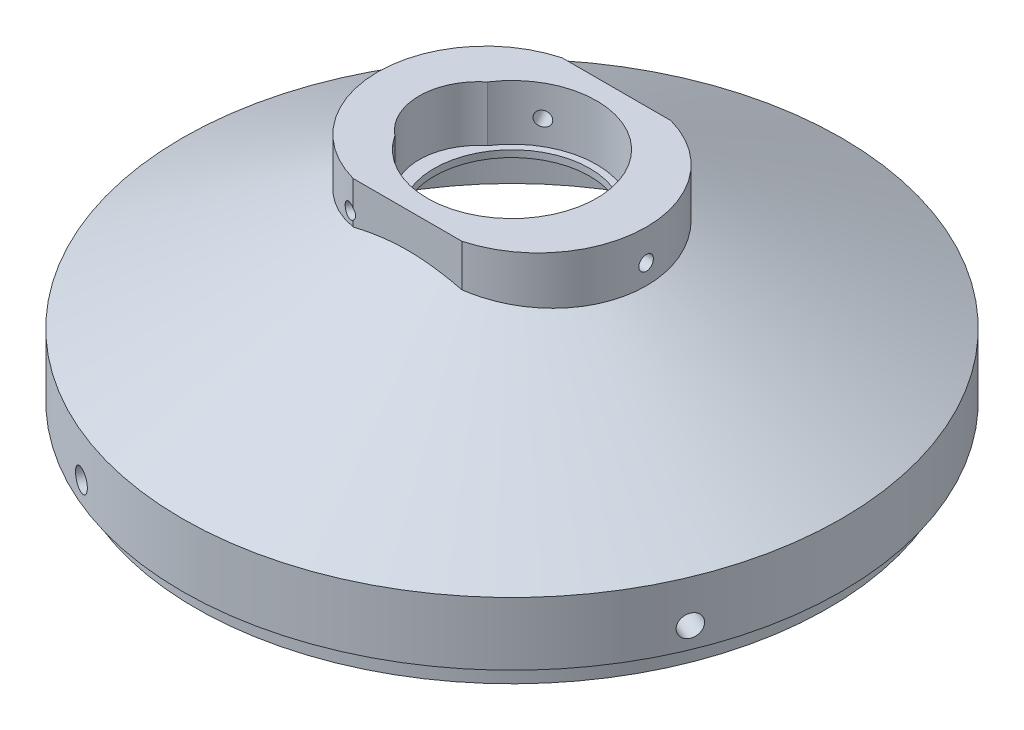
SolidWorks part; units mm, degrees
ref_plane "Front Plane" through (0, 0, 0) normal (0, 0, 1) x (1, 0, 0)
ref_plane "Top Plane" through (0, 0, 0) normal (0, 1, 0) x (1, 0, 0)
ref_plane "Right Plane" through (0, 0, 0) normal (1, 0, 0) x (0, 0, -1)
sketch "Sketch2" plane through (0, 0, 0) normal (0, 0, 1) x (1, 0, 0)
  line L0 (47.675, 0) -> (0, 0) construction
  line L1 (0, 0) -> (0, 12.7) construction
  line L2 (49.7, 12.7) -> (49.7, 3.2004)
  line L3 (49.7, 3.2004) -> (47.675, 3.2004)
  line L4 (47.675, 3.2004) -> (47.675, 0)
  line L5 (0, 12.7) -> (49.7, 12.7) construction
  line L6 (44.7, 9.6967) -> (44.7, 0)
  line L7 (44.7, 0) -> (47.675, 0)
  line L8 (28.725, 18.1967) -> (31.0736, 22.6107) construction
  line L9 (44.7, 0) -> (49.7, 0) construction
  line L10 (12.75, 26.6967) -> (11.73, 26.6967)
  line L11 (49.7, 12.7) -> (17.75, 29.7)
  line L12 (17.75, 29.7) -> (17.75, 36.04)
  line L13 (17.75, 36.04) -> (12.75, 36.04)
  line L14 (12.75, 36.04) -> (12.75, 27.7167)
  line L15 (12.75, 26.6967) -> (44.7, 9.6967)
  line L16 (11.73, 26.6967) -> (11.73, 27.7167)
  line L17 (11.73, 27.7167) -> (12.75, 27.7167)
  dimension "D1" = 49.7
  dimension "D2" = 2.025
  dimension "D3" = 9.4996
  dimension "D4" = 12.7
  dimension "D5" = 5
  dimension "D6" = 12.75
  dimension "D7" = 6.34
  dimension "D8" = 17
  dimension "D9" = 1.02
  dimension "D10" = 1.02
revolve "Revolve1" add sketch "Sketch2" angle 360 about L1
ref_axis "Axis1" through (0, 13.335, 0) along (0, -1, 0)
ref_plane "Plane1" through (0, 0, 0) normal (-0.3827, 0, 0.9239) x (0.9239, 0, 0.3827)
ref_plane "Plane2" through (0, 0, 0) normal (0.5878, 0, 0.809) x (0.809, 0, -0.5878)
sketch "Sketch12" plane through (0, 0, 0) normal (-0.3827, 0, 0.9239) x (0.9239, 0, 0.3827)
  line L0 (0, 12.7) -> (0, 0) construction
  line L1 (49.7, 12.7) -> (-49.7, 12.7) construction
  line L2 (-47.675, 0) -> (47.675, 0) construction
  line L3 (0, 13.335) -> (0, -0.635) construction
  circle A0 centre (0, 6.35) radius 1.6425
  dimension "D1" = 3.285
extrude "Cut-Extrude6" cut sketch "Sketch12" against normal through all
sketch "Sketch13" plane through (0, 36.04, 0) normal (0, 1, 0) x (1, 0, 0)
  line L1 (-8.1854, 15.75) -> (8.1854, 15.75)
  line L2 (-8.1854, 15.75) -> (-8.1854, 17.75)
  line L3 (-8.1854, 17.75) -> (8.1854, 17.75)
  line L4 (8.1854, 15.75) -> (8.1854, 17.75)
  line L5 (-8.1854, -15.75) -> (8.1854, -15.75)
  line L6 (-8.1854, -15.75) -> (-8.1854, -17.75)
  line L7 (-8.1854, -17.75) -> (8.1854, -17.75)
  line L8 (8.1854, -15.75) -> (8.1854, -17.75)
  circle A0 centre (0, 0) radius 17.75 construction
  circle A1 centre (0, 0) radius 17.75 construction
  dimension "D1" = 31.5
extrude "Cut-Extrude7" cut sketch "Sketch13" against normal up to surface (6.34 mm away) up to face at (0, 29.7, -17.75)
sketch "Sketch14" plane through (0, 36.04, 0) normal (0, 1, 0) x (1, 0, 0)
  line L0 (-8.1854, 0) -> (8.1854, 0) construction
  line L1 (-8.1854, 15.75) -> (8.1854, 15.75)
  line L2 (-8.1854, -15.75) -> (8.1854, -15.75)
  line L3 (8.1854, 15.75) -> (-8.1854, 15.75) construction
  line L4 (-8.1854, -15.75) -> (8.1854, -15.75) construction
  line L5 (20.25, 15.75) -> (20.25, -15.75) construction
  arc A0 (8.1854, 15.75) -> (8.1854, -15.75) centre (3.9371, 0) cw
  arc A1 (-8.1854, 15.75) -> (-8.1854, -15.75) centre (-3.9371, 0) ccw
  circle A2 centre (0, 0) radius 12.75
  circle A3 centre (0, 0) radius 12.75 construction
  point P2 (0, 0)
  point P20 (12.75, 0)
  dimension "D1" = 7.5
extrude "Boss-Extrude1" add sketch "Sketch14" against normal up to surface (6.34 mm away) up to face at (0, 29.7, 0)
sketch "Sketch15" plane through (0, 36.04, 0) normal (0, 1, 0) x (1, 0, 0)
  arc A0 (-10.6566, 7) -> (-10.6566, -7) centre (-4.9997, 0) ccw
  circle A1 centre (0, 0) radius 12.75 construction
  arc A3 (-10.6566, 7) -> (-10.6566, -7) centre (0, 0) ccw
  point P3 (-13.9997, 0)
  dimension "D2" = 9
  dimension "D1" = 14
extrude "Cut-Extrude8" cut sketch "Sketch15" against normal up to surface (8.3233 mm away) up to face at (0, 27.7167, -11.73)
sketch "Sketch16" plane through (0, 0, 0) normal (1, 0, 0) x (0, 0, -1)
  line L0 (0, 26.6967) -> (0, 36.04) construction
  line L3 (-12.75, 26.6967) -> (12.75, 26.6967) construction
  line L4 (0, 13.335) -> (0, -0.635) construction
  line L6 (12.75, 36.04) -> (-12.75, 36.04) construction
  circle A0 centre (0, 31.3683) radius 1.095
  dimension "D1" = 2.19
extrude "Cut-Extrude9" cut sketch "Sketch16" along normal through all
pattern_circular "CirPattern2" count 3 over 360 about axis through (0, 13.335, 0) along (0, -1, 0) of "Cut-Extrude9"
pattern_circular "CirPattern3" count 4 over 360 about axis through (0, 13.335, 0) along (0, -1, 0) of "Cut-Extrude6"
